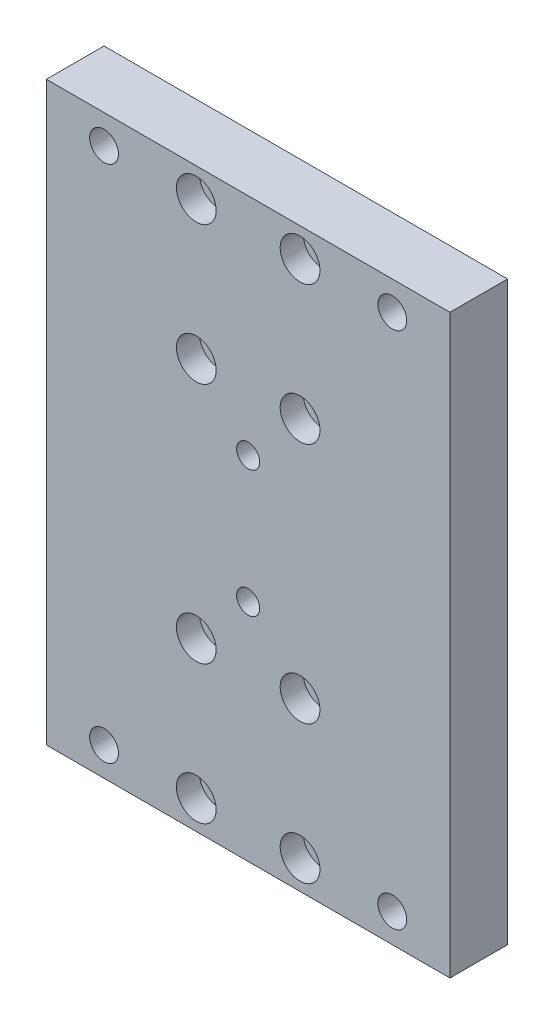
SolidWorks part; units mm, degrees
ref_plane "Front Plane" through (0, 0, 0) normal (0, 0, 1) x (1, 0, 0)
ref_plane "Top Plane" through (0, 0, 0) normal (0, 1, 0) x (1, 0, 0)
ref_plane "Right Plane" through (0, 0, 0) normal (1, 0, 0) x (0, 0, -1)
sketch "Sketch1" plane through (0, 0, 0) normal (0, 0, 1) x (1, 0, 0)
  line L1 (35, -50) -> (-35, -50)
  line L2 (35, -50) -> (35, 50)
  line L3 (35, 50) -> (-35, 50)
  line L4 (-35, -50) -> (-35, 50)
  line L5 (35, -50) -> (-35, 50) construction
  line L6 (35, 50) -> (-35, -50) construction
  point P0 (0, 0)
  dimension "D1" = 70
  dimension "D2" = 100
extrude "Boss-Extrude1" add sketch "Sketch1" along normal blind 10
sketch "Sketch2" plane through (0, 0, 0) normal (0, 0, -1) x (-1, 0, 0)
  line L0 (0, 50) -> (0, 0) construction
  line L1 (-35, 50) -> (35, 50) construction
  line L2 (0, 0) -> (-35, 0) construction
  line L3 (-35, -50) -> (-35, 50) construction
  circle A0 centre (-25, 45) radius 2.5
  circle A1 centre (25, 45) radius 2.5
  circle A2 centre (-25, -45) radius 2.5
  circle A3 centre (25, -45) radius 2.5
  dimension "D1" = 5
  dimension "D2" = 5
  dimension "D3" = 10
extrude "Cut-Extrude1" cut sketch "Sketch2" against normal through all
sketch "Sketch3" plane through (0, 0, 0) normal (0, 0, -1) x (-1, 0, 0)
  circle A1 centre (9, 21) radius 1.5
  circle A2 centre (9, 21) radius 1.5
  circle A3 centre (9, 45) radius 1.5
  circle A4 centre (9, 45) radius 1.5
  circle A5 centre (-9, 21) radius 1.5
  circle A6 centre (-9, 21) radius 1.5
  circle A7 centre (-9, 45) radius 1.5
  circle A8 centre (-9, 45) radius 1.5
  circle A9 centre (9, -45) radius 1.5
  circle A10 centre (9, -45) radius 1.5
  circle A11 centre (9, -21) radius 1.5
  circle A12 centre (9, -21) radius 1.5
  circle A13 centre (-9, -45) radius 1.5
  circle A14 centre (-9, -45) radius 1.5
  circle A15 centre (-9, -21) radius 1.5
  circle A16 centre (-9, -21) radius 1.5
  dimension "D1" = 0
  dimension "D2" = 0
  dimension "D3" = 0
  dimension "D4" = 0
  dimension "D5" = 0
  dimension "D6" = 0
  dimension "D7" = 0
  dimension "D8" = 0
extrude "Cut-Extrude2" cut sketch "Sketch3" against normal through all
sketch "Sketch4" plane through (0, 0, 10) normal (0, 0, 1) x (1, 0, 0)
  line L0 (0, 50) -> (0, 0) construction
  line L1 (35, 50) -> (-35, 50) construction
  line L2 (0, 0) -> (-35, 0) construction
  line L3 (-35, 50) -> (-35, -50) construction
  line L4 (0, 33) -> (-35, 33) construction
  circle A0 centre (-9, 45) radius 3.45
  circle A1 centre (-9, 21) radius 3.45
  circle A2 centre (9, 21) radius 3.45
  circle A3 centre (9, 45) radius 3.45
  circle A4 centre (9, -21) radius 3.45
  circle A5 centre (-9, -21) radius 3.45
  circle A6 centre (-9, -45) radius 3.45
  circle A7 centre (9, -45) radius 3.45
  dimension "D1" = 6.9
extrude "Cut-Extrude3" cut sketch "Sketch4" against normal blind 4
sketch "Sketch5" plane through (0, 0, 10) normal (0, 0, 1) x (1, 0, 0)
  circle A1 centre (0, -11) radius 2
  circle A2 centre (0, -11) radius 2
  circle A3 centre (0, 11) radius 2
  circle A4 centre (0, 11) radius 2
  dimension "D1" = 0
  dimension "D2" = 0
extrude "Cut-Extrude4" cut sketch "Sketch5" against normal through all
